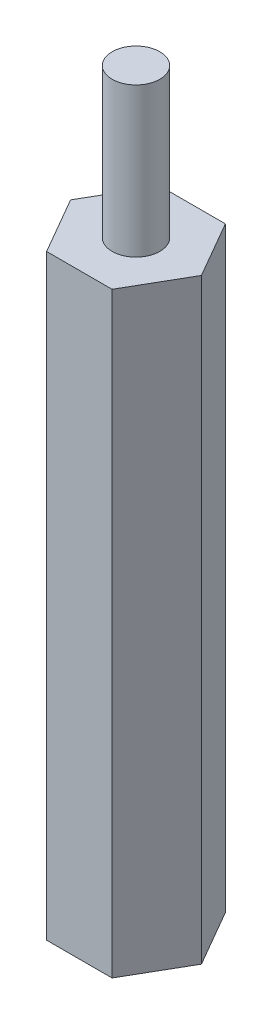
SolidWorks part; units mm, degrees
ref_plane "Front Plane" through (0, 0, 0) normal (0, 0, 1) x (1, 0, 0)
ref_plane "Top Plane" through (0, 0, 0) normal (0, 1, 0) x (1, 0, 0)
ref_plane "Right Plane" through (0, 0, 0) normal (1, 0, 0) x (0, 0, -1)
sketch "Sketch1" plane through (0, 0, 0) normal (0, 1, 0) x (1, 0, 0)
  line L1 (1.3931, -2.413) -> (2.7863, 0)
  line L2 (2.7863, 0) -> (1.3931, 2.413)
  line L3 (1.3931, 2.413) -> (-1.3931, 2.413)
  line L4 (-1.3931, 2.413) -> (-2.7863, 0)
  line L5 (-2.7863, 0) -> (-1.3931, -2.413)
  line L6 (-1.3931, -2.413) -> (1.3931, -2.413)
  circle A0 centre (0, 0) radius 2.413 construction
  dimension "D1" = 4.826
  dimension "D2" = 0
extrude "Boss-Extrude1" add sketch "Sketch1" along normal blind 25.4
sketch "Sketch2" plane through (0, 25.4, 0) normal (0, 1, 0) x (1, 0, 0)
  circle A0 centre (0, 0) radius 1.016
  dimension "D1" = 2.032
extrude "Boss-Extrude2" add sketch "Sketch2" along normal blind 6.35
sketch "Sketch3" plane through (0, 0, 0) normal (0, -1, 0) x (1, 0, 0)
  circle A0 centre (0, 0) radius 1.016
  dimension "D1" = 2.032
extrude "Cut-Extrude1" cut sketch "Sketch3" against normal blind 6.35
